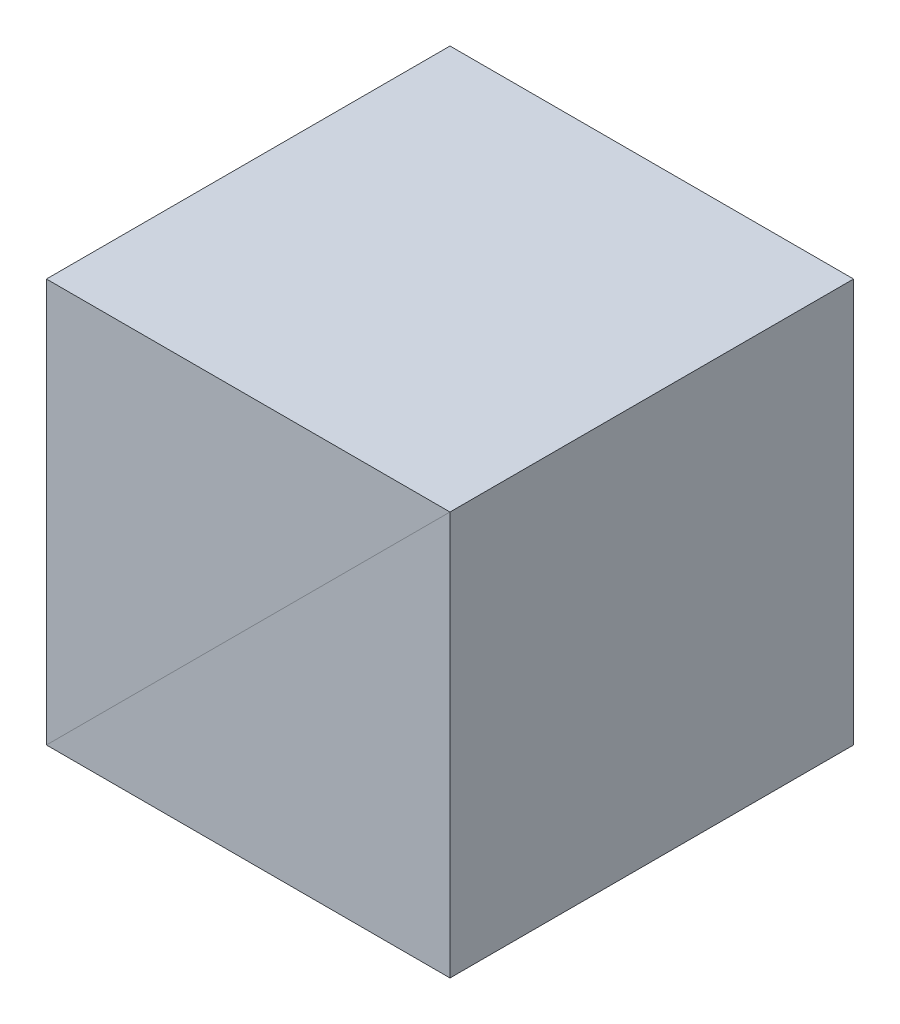
SolidWorks part; units mm, degrees
ref_plane "前视基准面" through (0, 0, 0) normal (0, 0, 1) x (1, 0, 0)
ref_plane "上视基准面" through (0, 0, 0) normal (0, 1, 0) x (1, 0, 0)
ref_plane "右视基准面" through (0, 0, 0) normal (1, 0, 0) x (0, 0, -1)
sketch "草图1" plane through (0, 0, 0) normal (0, 0, 1) x (1, 0, 0)
  line L3 (-10, -10) -> (10, -10)
  line L4 (10, 10) -> (10, -10)
  line L5 (10, 10) -> (-10, -10)
  dimension "D1" = 20
extrude "凸台-拉伸1" add sketch "草图1" along normal mid plane 20
mirror "镜向2" about plane through (10, 10, 10) normal (0.7071, -0.7071, 0) of bodies 107
